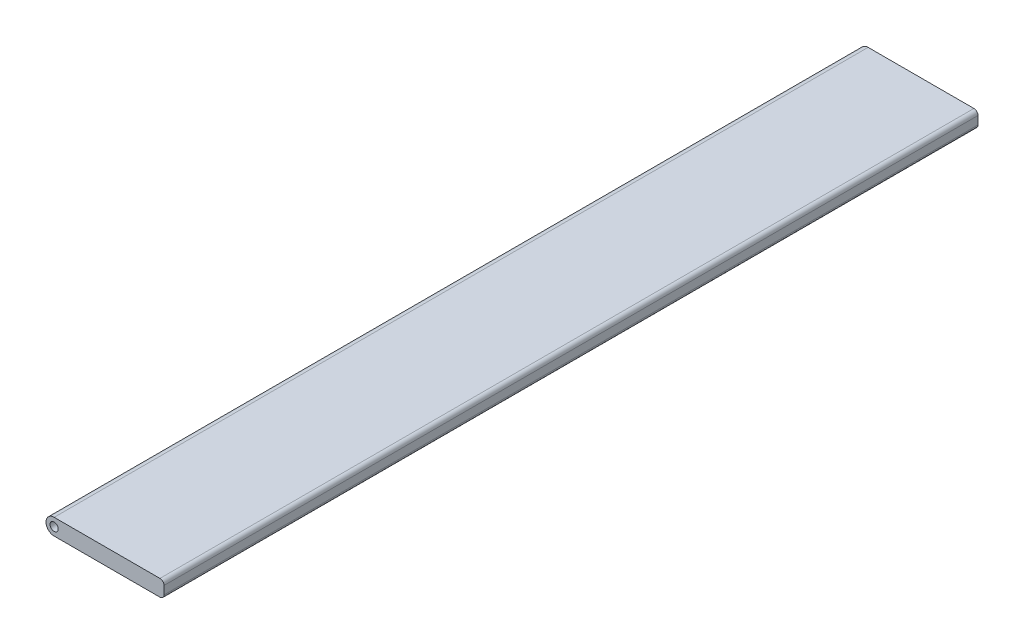
SolidWorks part; units mm, degrees
ref_plane "Front" through (0, 0, 0) normal (0, 0, 1) x (1, 0, 0)
ref_plane "Top" through (0, 0, 0) normal (0, 1, 0) x (1, 0, 0)
ref_plane "Right" through (0, 0, 0) normal (1, 0, 0) x (0, 0, -1)
sketch "草图1" plane through (0, 0, 0) normal (0, 0, 1) x (1, 0, 0)
  line L1 (0, -2) -> (26, -2)
  line L2 (0, -2) -> (0, 2)
  line L3 (0, 2) -> (26, 2)
  line L4 (27, -1) -> (27, 1)
  circle A0 centre (0, 0) radius 2
  arc A1 (26, -2) -> (27, -1) centre (26, -1) ccw
  circle A2 centre (0, 0) radius 1
  arc A3 (26, 2) -> (27, 1) centre (26, 1) cw
  point P12 (27, 2)
  dimension "D3" = 2
  dimension "D1" = 4
  dimension "D4" = 1
  dimension "D2" = 27
extrude "凸台-拉伸1" add sketch "草图1" along normal blind 200
